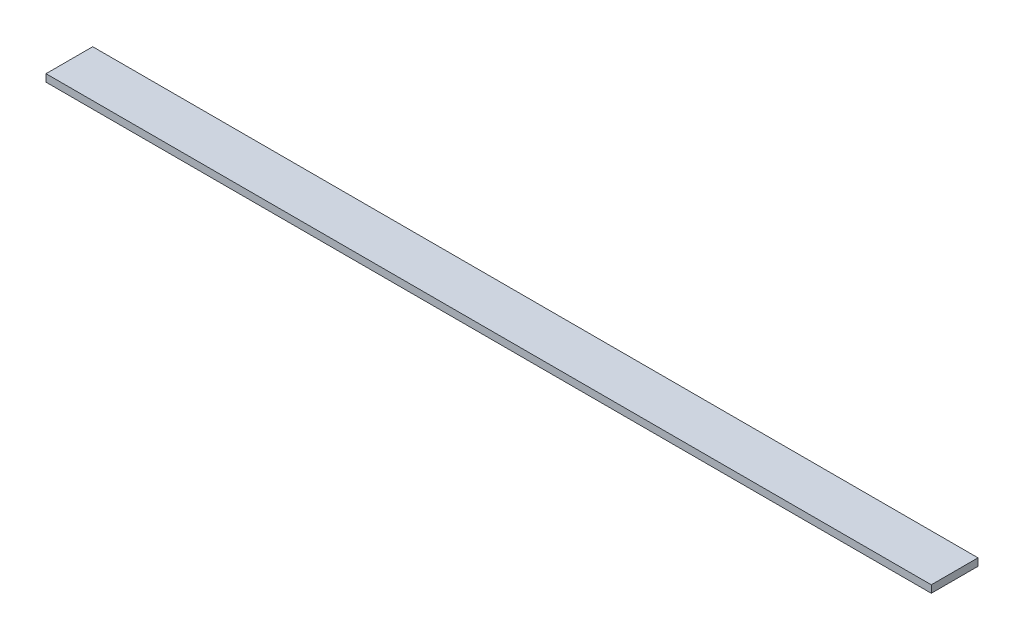
SolidWorks part; units mm, degrees
ref_plane "Front" through (0, 0, 0) normal (0, 0, 1) x (1, 0, 0)
ref_plane "Top" through (0, 0, 0) normal (0, 1, 0) x (1, 0, 0)
ref_plane "Right" through (0, 0, 0) normal (1, 0, 0) x (0, 0, -1)
sketch "Sketch1" plane through (0, 0, 0) normal (0, 1, 0) x (1, 0, 0)
  line L1 (-900, 47.5) -> (900, 47.5)
  line L2 (-900, 47.5) -> (-900, -47.5)
  line L3 (-900, -47.5) -> (900, -47.5)
  line L4 (900, 47.5) -> (900, -47.5)
  line L5 (-900, 47.5) -> (900, -47.5) construction
  line L6 (-900, -47.5) -> (900, 47.5) construction
  point P0 (0, 0)
  dimension "D1" = 1800
  dimension "D2" = 95
extrude "Boss-Extrude1" add sketch "Sketch1" along normal blind 15
